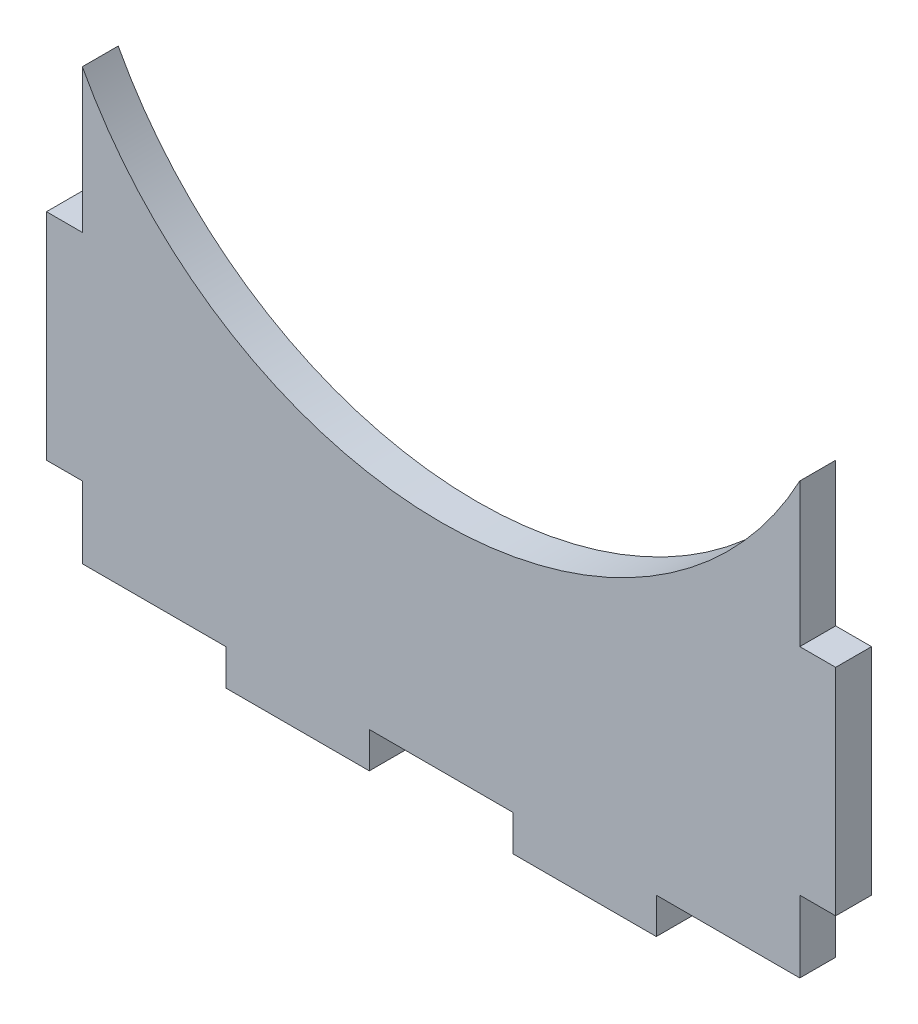
SolidWorks part; units mm, degrees
material "Pine"
ref_plane "Front Plane" through (0, 0, 0) normal (0, 0, 1) x (1, 0, 0)
ref_plane "Top Plane" through (0, 0, 0) normal (0, 1, 0) x (1, 0, 0)
ref_plane "Right Plane" through (0, 0, 0) normal (1, 0, 0) x (0, 0, -1)
sketch "Sketch1" plane through (0, 0, 0) normal (0, 0, 1) x (1, 0, 0)
  line L0 (0, 0) -> (0, 116.4167) construction
  line L3 (63.5, 6.35) -> (63.5, 19.05)
  line L4 (-63.5, 6.35) -> (-63.5, 19.05)
  line L5 (-63.5, 6.35) -> (-38.1, 6.35)
  line L6 (-12.7, 6.35) -> (12.7, 6.35)
  line L8 (-38.1, 6.35) -> (-38.1, 0)
  line L9 (-38.1, 0) -> (-12.7, 0)
  line L10 (-12.7, 6.35) -> (-12.7, 0)
  line L12 (38.1, 6.35) -> (38.1, 0)
  line L13 (38.1, 0) -> (12.7, 0)
  line L14 (12.7, 6.35) -> (12.7, 0)
  line L15 (38.1, 6.35) -> (63.5, 6.35)
  line L17 (-63.5, 57.15) -> (-69.85, 57.15)
  line L19 (-63.5, 19.05) -> (-69.85, 19.05)
  line L20 (-69.85, 57.15) -> (-69.85, 19.05)
  line L21 (-31.7103, 6.35) -> (-107.95, 6.35) construction
  line L22 (-63.5, 57.15) -> (-63.5, 82.55)
  line L23 (63.5, 19.05) -> (69.85, 19.05)
  line L24 (69.85, 57.15) -> (69.85, 19.05)
  line L25 (63.5, 57.15) -> (69.85, 57.15)
  line L26 (63.5, 57.15) -> (63.5, 82.55)
  line L28 (63.5, 6.35) -> (63.5, 0) construction
  arc A0 (-63.5, 82.55) -> (63.5, 82.55) centre (0, 116.4167) ccw
  point P33 (0, 44.45)
  dimension "D1" = 38.1
  dimension "D2" = 76.2
  dimension "D3" = 38.1
  dimension "D4" = 12.7
  dimension "D5" = 6.35
extrude "Boss-Extrude1" add sketch "Sketch1" along normal up to surface (6.35 mm away)
